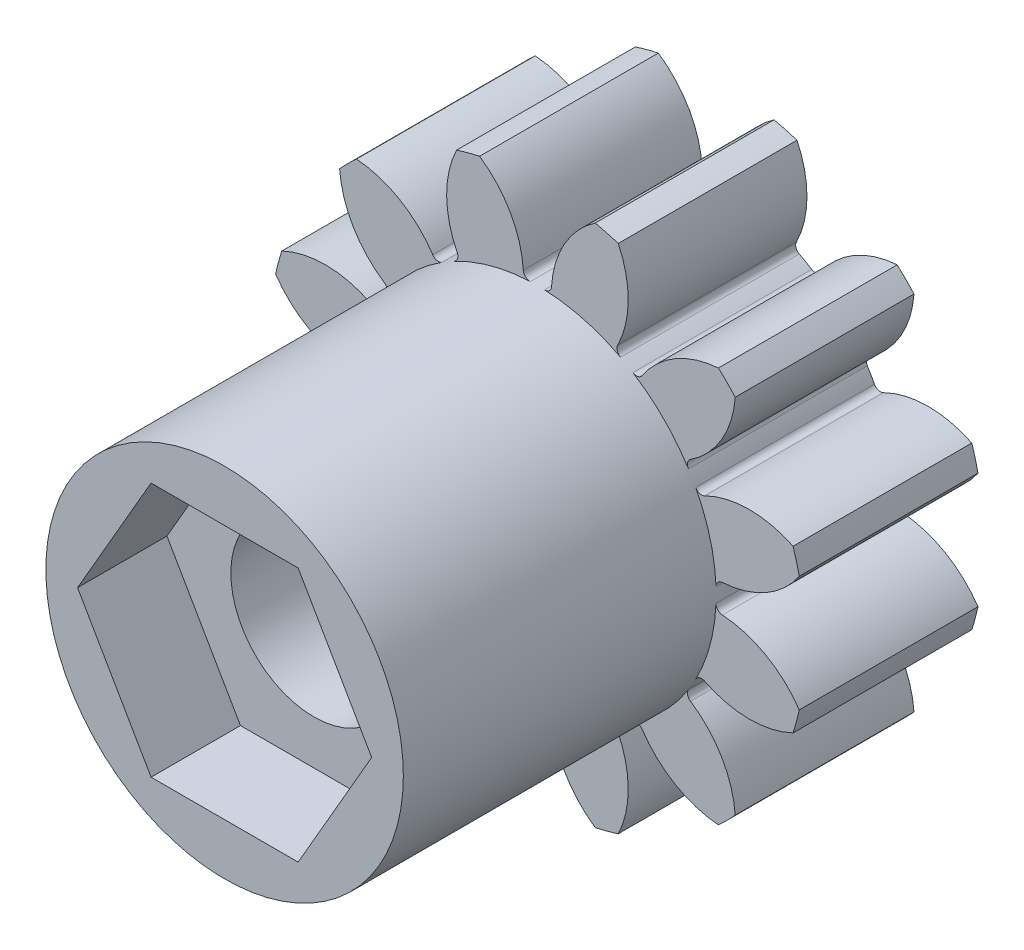
SolidWorks part; units mm, degrees
ref_plane "Front" through (0, 0, 0) normal (0, 0, 1) x (1, 0, 0)
ref_plane "Top" through (0, 0, 0) normal (0, 1, 0) x (1, 0, 0)
ref_plane "Right" through (0, 0, 0) normal (1, 0, 0) x (0, 0, -1)
sketch "Sketch1" plane through (0, 0, 0) normal (0, 0, 1) x (1, 0, 0)
  circle A0 centre (0, 0) radius 2
  circle A1 centre (0, 0) radius 6
extrude "Boss-Extrude1" add sketch "Sketch1" along normal blind 4
sketch "Sketch4" plane through (0, 0, 0) normal (0, 0, 1) x (1, 0, 0)
  arc A0 (-0.1602, 3.9968) -> (-0.3159, 4.1375) centre (-0.1662, 4.1467) cw
  arc A1 (0.1602, 3.9968) -> (-0.1602, 3.9968) centre (0, 0) ccw
  arc A2 (-0.3159, 4.1375) -> (-2.0102, 6.1814) centre (-2.5617, 4) ccw
  arc A3 (2.0102, 6.1814) -> (0.3159, 4.1375) centre (2.5617, 4) ccw
  arc A4 (0.1602, 3.9968) -> (0.3159, 4.1375) centre (0.1662, 4.1467) ccw
  arc A5 (2.0102, 6.1814) -> (-2.0102, 6.1814) centre (0, 0) ccw
  dimension "D1" = 0.15
  dimension "D2" = 0.15
extrude "Cut-Extrude2" cut sketch "Sketch4" along normal through all
pattern_circular "CirPattern2" count 12 over 360 about axis through (0, 0, 0) along (0, 0, 1) of "Cut-Extrude2"
sketch "Sketch10" plane through (0, 0, 0) normal (0, 0, 1) x (1, 0, 0)
  line L0 (0, 4) -> (-5.1235, 4) construction
  line L1 (0, 4) -> (5.1235, 4) construction
  circle A0 centre (0, 0) radius 6.5
  circle A1 centre (0, 0) radius 4
  circle A2 centre (-2.5617, 4) radius 2.25
  circle A3 centre (2.5617, 4) radius 2.25
sketch "Sketch11" plane through (0, 0, 0) normal (0, 0, 1) x (1, 0, 0)
  circle A0 centre (0, 0) radius 4
extrude "Boss-Extrude2" add sketch "Sketch11" along normal blind 11
sketch "Sketch12" plane through (0, 0, 0) normal (0, 0, 1) x (1, 0, 0)
  line L1 (3.2909, 0) -> (1.6454, 2.85)
  line L2 (1.6454, 2.85) -> (-1.6454, 2.85)
  line L3 (-1.6454, 2.85) -> (-3.2909, 0)
  line L4 (-3.2909, 0) -> (-1.6454, -2.85)
  line L5 (-1.6454, -2.85) -> (1.6454, -2.85)
  line L6 (1.6454, -2.85) -> (3.2909, 0)
  circle A0 centre (0, 0) radius 2.85 construction
  dimension "D1" = 5.7
extrude "Cut-Extrude3" cut sketch "Sketch12" against normal blind 2 from offset 11
sketch "Sketch13" plane through (0, 0, 0) normal (0, 0, 1) x (1, 0, 0)
  line L0 (0, 0) -> (0, 0.95) construction
  line L2 (1.6, 0.95) -> (-1.6, 0.95)
  arc A0 (1.6, 0.95) -> (-1.6, 0.95) centre (0, 0) cw
extrude "Cut-Extrude4" cut sketch "Sketch13" along normal through all
